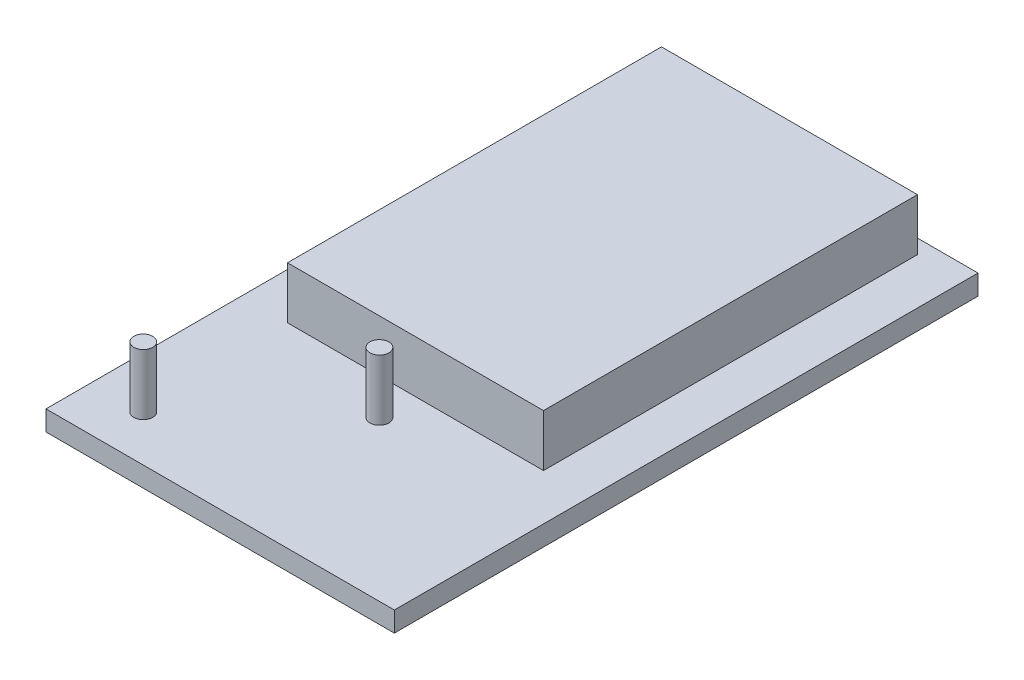
SolidWorks part; units mm, degrees
ref_plane "Front Plane" through (0, 0, 0) normal (0, 0, 1) x (1, 0, 0)
ref_plane "Top Plane" through (0, 0, 0) normal (0, 1, 0) x (1, 0, 0)
ref_plane "Right Plane" through (0, 0, 0) normal (1, 0, 0) x (0, 0, -1)
sketch "Sketch1" plane through (0, 0, 0) normal (0, 1, 0) x (1, 0, 0)
  line L1 (42.735, -71.6) -> (-42.735, -71.6)
  line L2 (42.735, -71.6) -> (42.735, 71.6)
  line L3 (42.735, 71.6) -> (-42.735, 71.6)
  line L4 (-42.735, -71.6) -> (-42.735, 71.6)
  line L5 (42.735, -71.6) -> (-42.735, 71.6) construction
  line L6 (42.735, 71.6) -> (-42.735, -71.6) construction
  point P0 (0, 0)
  dimension "D1" = 85.47
  dimension "D2" = 143.2
extrude "Boss-Extrude1" add sketch "Sketch1" along normal blind 4.92
sketch "Sketch2" plane through (0, 4.92, 0) normal (0, 1, 0) x (1, 0, 0)
  line L0 (-42.735, 71.6) -> (-42.735, -71.6) construction
  line L1 (-31.405, 68.08) -> (31.405, 68.08)
  line L2 (-31.405, 68.08) -> (-31.405, -23.68)
  line L3 (-31.405, -23.68) -> (31.405, -23.68)
  line L4 (31.405, 68.08) -> (31.405, -23.68)
  line L5 (-31.405, 68.08) -> (31.405, -23.68) construction
  line L6 (-31.405, -23.68) -> (31.405, 68.08) construction
  line L8 (-42.735, -71.6) -> (42.735, -71.6) construction
  point P0 (0, 22.2)
  dimension "D1" = 47.92
  dimension "D2" = 91.76
  dimension "D3" = 11.33
extrude "Boss-Extrude2" add sketch "Sketch2" along normal blind 12.75
sketch "Sketch3" plane through (0, 4.92, 0) normal (0, 1, 0) x (1, 0, 0)
  line L0 (-31.405, -23.68) -> (31.405, -23.68) construction
  circle A0 centre (0, -32.53) radius 2.33
  circle A1 centre (-30.1569, -60.3139) radius 2.33
  dimension "D1" = 4.66
  dimension "D2" = 8.85
extrude "Boss-Extrude3" add sketch "Sketch3" along normal blind 14.9
